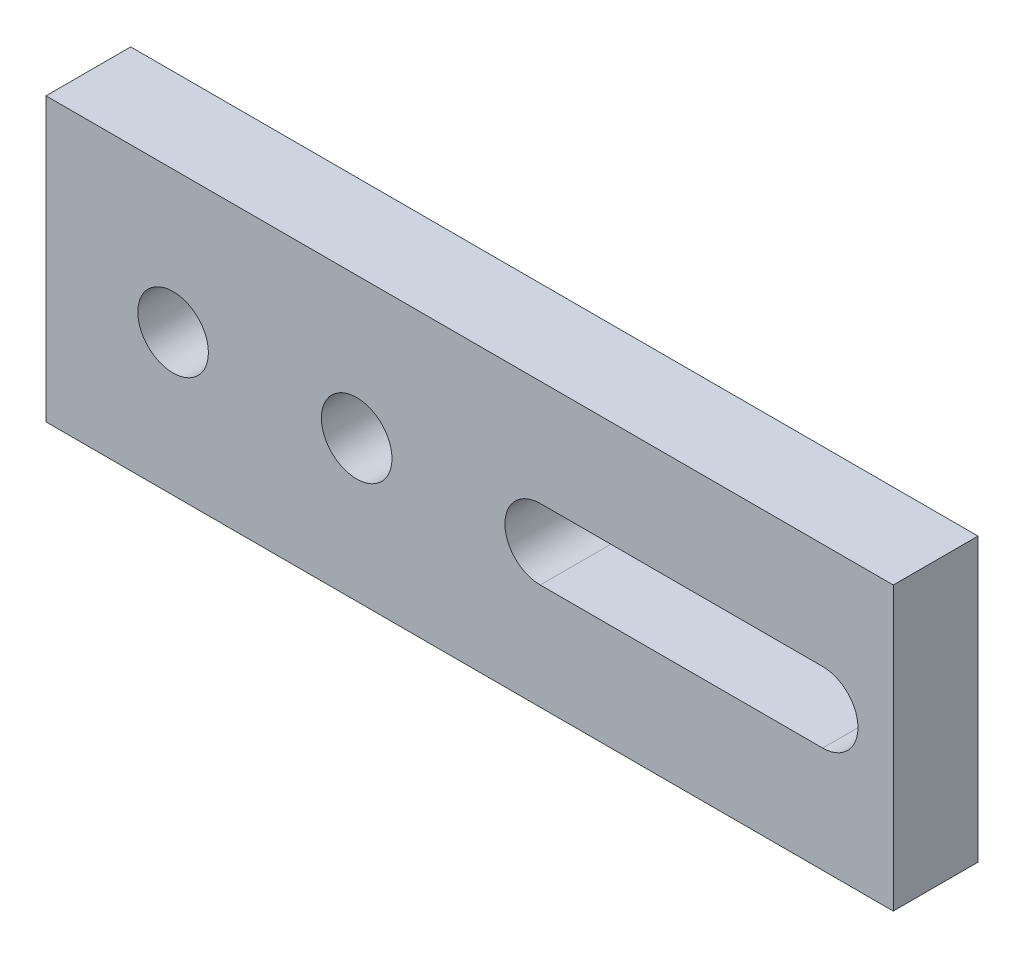
SolidWorks part; units mm, degrees
ref_plane "Front Plane" through (0, 0, 0) normal (0, 0, 1) x (1, 0, 0)
ref_plane "Top Plane" through (0, 0, 0) normal (0, 1, 0) x (1, 0, 0)
ref_plane "Right Plane" through (0, 0, 0) normal (1, 0, 0) x (0, 0, -1)
sketch "Sketch1" plane through (0, 0, 0) normal (0, 0, 1) x (1, 0, 0)
  line L0 (35, 10) -> (55, 10) construction
  line L1 (0, 0) -> (60, 0)
  line L2 (0, 0) -> (0, 20)
  line L3 (0, 20) -> (60, 20)
  line L4 (60, 0) -> (60, 20)
  line L5 (35, 12.5) -> (55, 12.5)
  line L6 (35, 7.5) -> (55, 7.5)
  arc A0 (35, 12.5) -> (35, 7.5) centre (35, 10) ccw
  arc A1 (55, 7.5) -> (55, 12.5) centre (55, 10) ccw
  circle A2 centre (22, 10) radius 2.5
  circle A3 centre (9, 10) radius 2.5
  point P7 (45, 10)
  point P12 (60, 10)
  dimension "D4" = 2.5
  dimension "D7" = 5
  dimension "D8" = 5
  dimension "D1" = 20
  dimension "D2" = 60
  dimension "D3" = 20
  dimension "D5" = 5
  dimension "D6" = 0
  dimension "D9" = 13
  dimension "D10" = 13
extrude "Boss-Extrude1" add sketch "Sketch1" along normal blind 6
